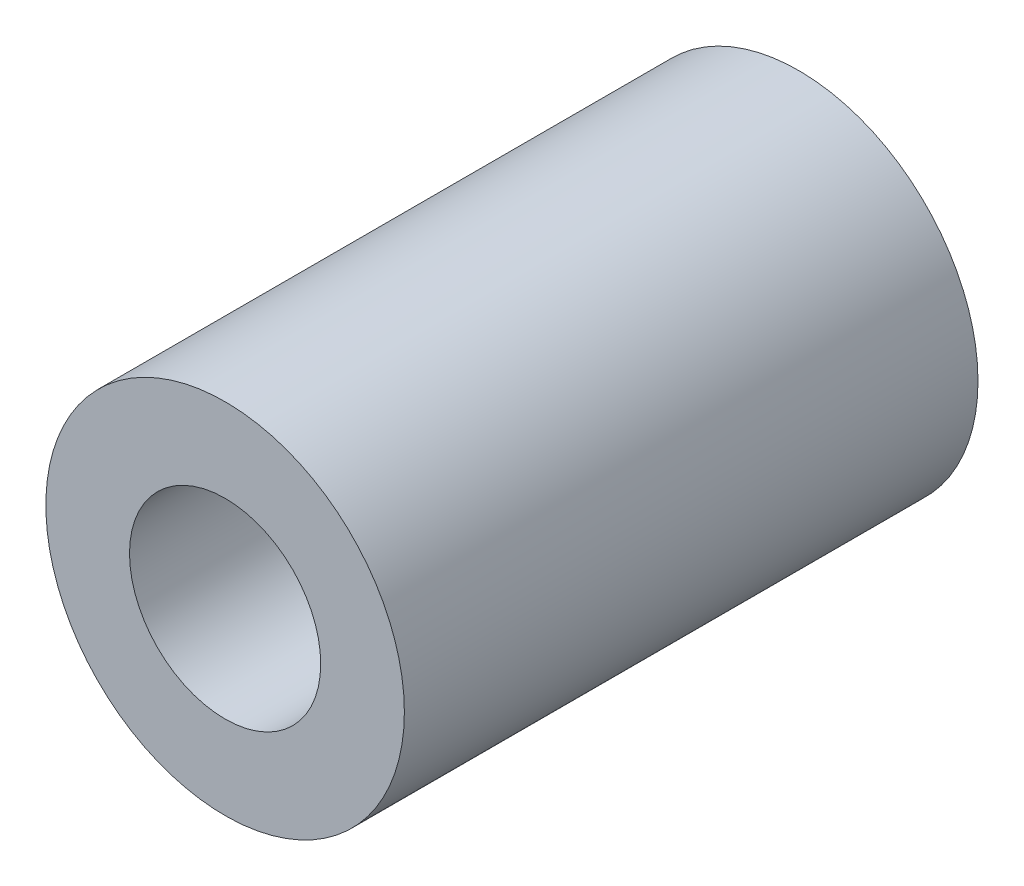
SolidWorks part; units mm, degrees
ref_plane "Front Plane" through (0, 0, 0) normal (0, 0, 1) x (1, 0, 0)
ref_plane "Top Plane" through (0, 0, 0) normal (0, 1, 0) x (1, 0, 0)
ref_plane "Right Plane" through (0, 0, 0) normal (1, 0, 0) x (0, 0, -1)
sketch "Sketch1" plane through (0, 0, 0) normal (0, 0, 1) x (1, 0, 0)
  circle A0 centre (0, 0) radius 4
  circle A1 centre (0, 0) radius 7.5
  dimension "D1" = 15
  dimension "D2" = 8
extrude "Boss-Extrude1" add sketch "Sketch1" along normal blind 24
